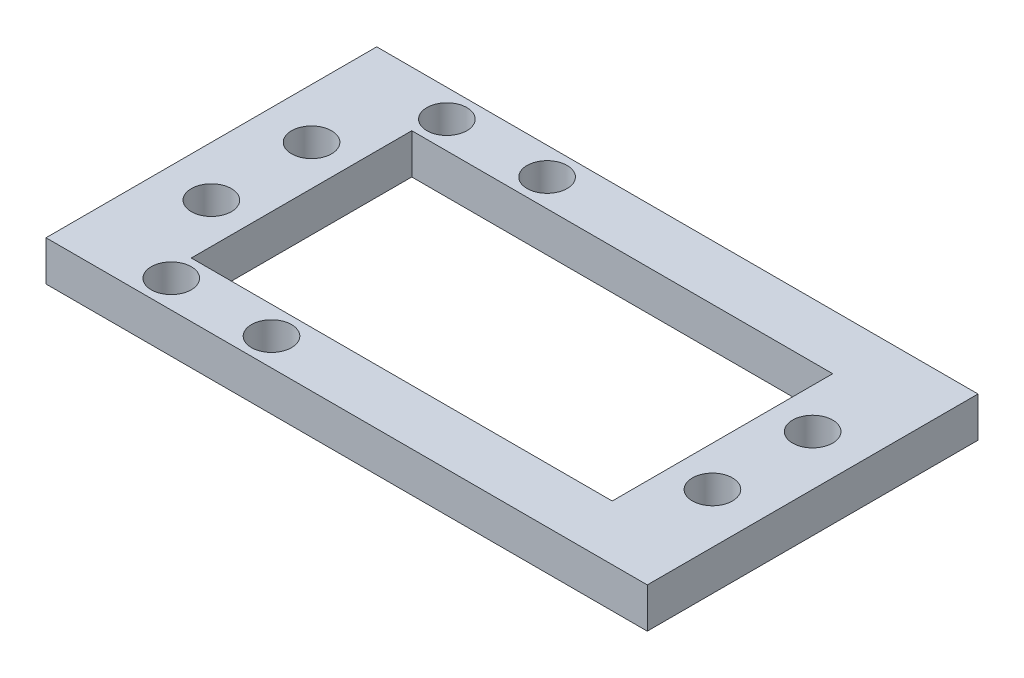
SolidWorks part; units mm, degrees
ref_plane "Alzado" through (0, 0, 0) normal (0, 0, 1) x (1, 0, 0)
ref_plane "Planta" through (0, 0, 0) normal (0, 1, 0) x (1, 0, 0)
ref_plane "Vista lateral" through (0, 0, 0) normal (1, 0, 0) x (0, 0, -1)
sketch "Croquis2" plane through (0, 0, 0) normal (0, 0, 1) x (1, 0, 0)
  line L0 (-40.0265, 0) -> (59.1402, 0) construction
  line L1 (-31.1459, -11.0012) -> (-31.1459, 23.9988)
  line L2 (-31.1459, 23.9988) -> (53.8541, 23.9988)
  line L3 (53.8541, 23.9988) -> (53.8541, -11.0012)
  line L4 (-31.1459, -11.0012) -> (-35.1459, -11.0012)
  line L5 (-35.1459, -11.0012) -> (-35.1459, 27.9988)
  line L6 (53.8541, -11.0012) -> (57.8541, -11.0012)
  line L7 (57.8541, -11.0012) -> (57.8541, 27.9988)
  line L8 (57.8541, 27.9988) -> (-35.1459, 27.9988)
  dimension "D1" = 85
  dimension "D2" = 35
  dimension "D3" = 35
  dimension "D4" = 4
  dimension "D5" = 39
  dimension "D6" = 4
extrude "Saliente-Extruir1" add sketch "Croquis2" along normal blind 40
sketch "Croquis3" plane through (-35.1459, 0, 0) normal (-1, 0, 0) x (0, 0, 1)
  line L0 (40, 27.9988) -> (0, 27.9988) construction
  circle A0 centre (20, 7.9988) radius 2.5
  dimension "D1" = 5
  dimension "D2" = 25
extrude "Cortar-Extruir1" cut sketch "Croquis3" against normal through all
sketch "Croquis5" plane through (-35.1459, 0, 0) normal (-1, 0, 0) x (0, 0, 1)
  line L0 (0, 27.9988) -> (0, -11.0012) construction
  line L1 (40, -11.0012) -> (0, -11.0012)
  line L2 (40, -11.0012) -> (40, -1.0012)
  line L3 (40, -1.0012) -> (0, -1.0012)
  line L4 (0, -11.0012) -> (0, -1.0012)
  dimension "D1" = 10
extrude "Cortar-Extruir2" cut sketch "Croquis5" against normal blind 40
sketch "Croquis6" plane through (0, 27.9988, 0) normal (0, 1, 0) x (1, 0, 0)
  line L0 (-35.1459, -40) -> (-35.1459, 0) construction
  line L1 (-9.6459, -9) -> (32.3541, -9)
  line L2 (-9.6459, -9) -> (-9.6459, -31)
  line L3 (-9.6459, -31) -> (32.3541, -31)
  line L4 (32.3541, -9) -> (32.3541, -31)
  line L5 (-9.6459, -9) -> (32.3541, -31) construction
  line L6 (-9.6459, -31) -> (32.3541, -9) construction
  point P0 (11.3541, -20)
  point P10 (-35.1459, -20)
  dimension "D1" = 42
  dimension "D2" = 46.5
  dimension "D3" = 22
extrude "Cortar-Extruir3" cut sketch "Croquis6" against normal blind 10
sketch "Croquis7" plane through (0, 27.9988, 0) normal (0, 1, 0) x (1, 0, 0)
  line L0 (-15.6459, 6.5811) -> (-15.6459, -45.5911) construction
  line L1 (-9.6459, -9) -> (-9.6459, -31) construction
  line L2 (-9.6459, -20) -> (32.3541, -20) construction
  line L3 (38.3541, 7.3731) -> (38.3541, -50.5411) construction
  line L4 (32.3541, -31) -> (32.3541, -9) construction
  circle A0 centre (-13.6459, -15) radius 2
  circle A1 centre (-13.6459, -25) radius 2
  circle A2 centre (36.3541, -15) radius 2
  circle A3 centre (36.3541, -25) radius 2
  dimension "D1" = 4
  dimension "D2" = 4
  dimension "D3" = 4
  dimension "D4" = 4
  dimension "D5" = 4
  dimension "D6" = 4
  dimension "D7" = 5
  dimension "D8" = 5
  dimension "D9" = 5
  dimension "D10" = 5
  dimension "D11" = 6
  dimension "D12" = 6
extrude "Cortar-Extruir4" cut sketch "Croquis7" against normal blind 10
sketch "Croquis8" plane through (0, 27.9988, 0) normal (0, 1, 0) x (1, 0, 0)
  line L0 (11.3541, -9) -> (11.3541, -31) construction
  line L1 (32.3541, -9) -> (-9.6459, -9) construction
  line L2 (-9.6459, -31) -> (32.3541, -31) construction
  line L3 (11.3541, -20) -> (-18.6459, -20) construction
  line L4 (-9.6459, -9) -> (11.3541, -9) construction
  line L5 (-18.6459, -36.5) -> (41.3541, -36.5)
  line L6 (-18.6459, -36.5) -> (-18.6459, -3.5)
  line L7 (-18.6459, -3.5) -> (41.3541, -3.5)
  line L8 (41.3541, -36.5) -> (41.3541, -3.5)
  line L9 (-18.6459, -36.5) -> (41.3541, -3.5) construction
  line L10 (-18.6459, -3.5) -> (41.3541, -36.5) construction
  line L11 (0.8541, -9) -> (0.8541, -3.5) construction
  line L12 (0.8541, -6.25) -> (-18.6459, -6.25) construction
  line L13 (-13.6459, -25) -> (-13.6459, -15) construction
  line L15 (-9.6459, -31) -> (32.3541, -31)
  line L16 (-9.6459, -31) -> (-9.6459, -9)
  line L17 (-9.6459, -9) -> (32.3541, -9)
  line L18 (32.3541, -31) -> (32.3541, -9)
  line L19 (-9.6459, -31) -> (32.3541, -9) construction
  line L20 (-9.6459, -9) -> (32.3541, -31) construction
  line L25 (-37.0442, -48.9606) -> (59.7524, 8.9606) construction
  line L26 (-37.0442, 8.9606) -> (59.7524, -48.9606) construction
  circle A1 centre (-8.8959, -6.25) radius 2
  circle A2 centre (1.1041, -6.25) radius 2
  circle A4 centre (-8.8959, -33.75) radius 2
  circle A5 centre (1.1041, -33.75) radius 2
  circle A6 centre (-13.6459, -15) radius 2
  circle A7 centre (-13.6459, -25) radius 2
  circle A8 centre (36.3541, -15) radius 2
  circle A9 centre (36.3541, -25) radius 2
  dimension "D1" = 4
  dimension "D2" = 33
  dimension "D3" = 60
  dimension "D4" = 2
extrude "Saliente-Extruir2" add sketch "Croquis8" along normal blind 4
sketch "Croquis9" plane through (0, 0, 40) normal (0, 0, 1) x (1, 0, 0)
  line L1 (-35.1459, 27.9988) -> (64.7783, 27.9988)
  line L2 (-35.1459, 27.9988) -> (-35.1459, -28.8129)
  line L3 (-35.1459, -28.8129) -> (64.7783, -28.8129)
  line L4 (64.7783, 27.9988) -> (64.7783, -28.8129)
extrude "Cortar-Extruir9" cut sketch "Croquis9" against normal through all
